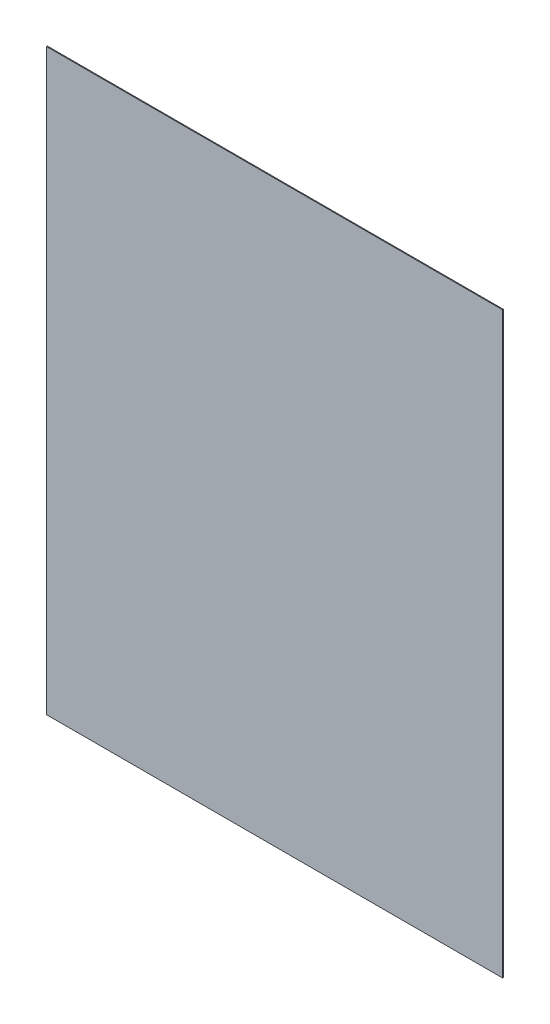
SolidWorks part; units mm, degrees
ref_plane "Front Plane" through (0, 0, 0) normal (0, 0, 1) x (1, 0, 0)
ref_plane "Top Plane" through (0, 0, 0) normal (0, 1, 0) x (1, 0, 0)
ref_plane "Right Plane" through (0, 0, 0) normal (1, 0, 0) x (0, 0, -1)
sketch "Sketch1" plane through (0, 0, 0) normal (0, 0, 1) x (1, 0, 0)
  line L1 (-260.5, -330.5) -> (260.5, -330.5)
  line L2 (-260.5, -330.5) -> (-260.5, 330.5)
  line L3 (-260.5, 330.5) -> (260.5, 330.5)
  line L4 (260.5, -330.5) -> (260.5, 330.5)
  line L5 (-260.5, -330.5) -> (260.5, 330.5) construction
  line L6 (-260.5, 330.5) -> (260.5, -330.5) construction
  point P0 (0, 0)
  dimension "D1" = 661
  dimension "D2" = 521
extrude "Boss-Extrude1" add sketch "Sketch1" along normal blind 1
